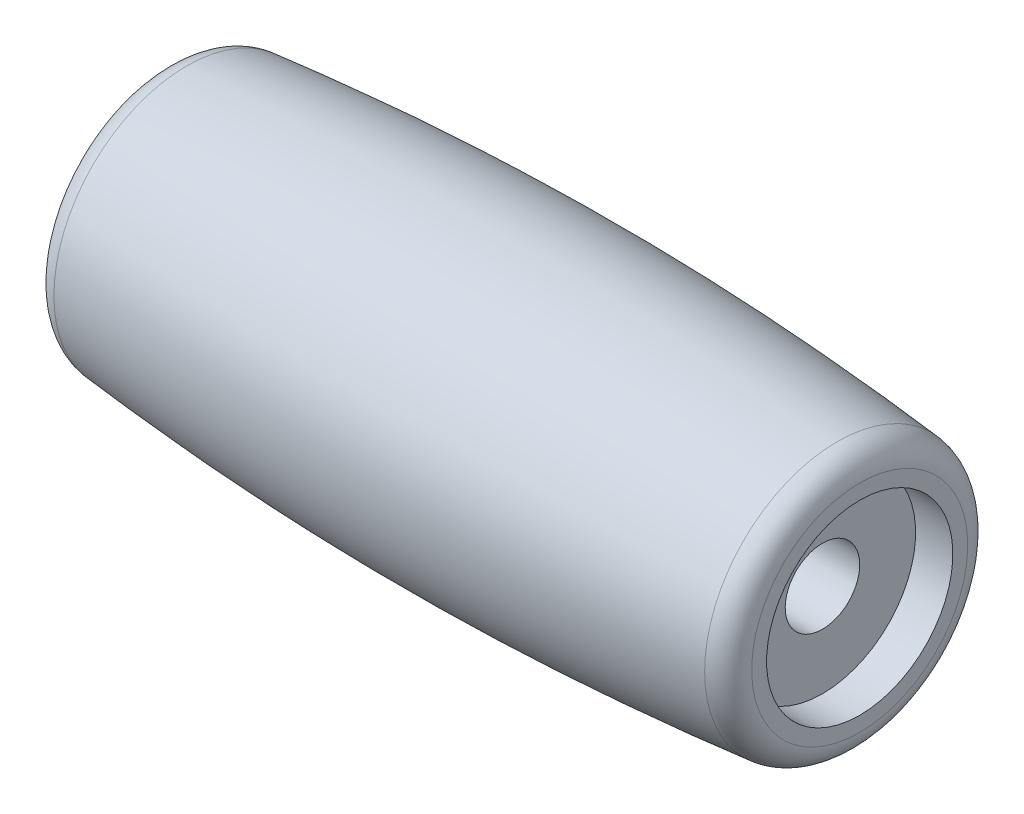
SolidWorks part; units mm, degrees
material "Nylon 101"
ref_plane "Front Plane" through (0, 0, 0) normal (0, 0, 1) x (1, 0, 0)
ref_plane "Top Plane" through (0, 0, 0) normal (0, 1, 0) x (1, 0, 0)
ref_plane "Right Plane" through (0, 0, 0) normal (1, 0, 0) x (0, 0, -1)
sketch "Sketch1" plane through (0, 0, 0) normal (0, 0, 1) x (1, 0, 0)
  line L0 (-75, 0) -> (75, 0) construction
  line L3 (0, 0) -> (0, 6) construction
  line L5 (0, 0) -> (0, 30) construction
  line L6 (-12.5, 1.5) -> (12.5, 1.5)
  line L7 (12.5, 1.5) -> (12.5, 3.75)
  line L8 (12.5, 3.75) -> (14, 3.75)
  line L9 (14, 3.75) -> (14, 4.3484)
  line L10 (-14, 3.75) -> (-14, 4.3484)
  line L11 (-12.5, 3.75) -> (-14, 3.75)
  line L12 (-12.5, 1.5) -> (-12.5, 3.75)
  arc A0 (14, 4.3484) -> (13.0998, 5.3434) centre (13, 4.3484) ccw
  arc A1 (-14, 4.3484) -> (-13.0998, 5.3434) centre (-13, 4.3484) cw
  spline S0 degree 3 poles (13.0998, 5.3434) (8.7333, 5.7813) (0.0007, 6.2188) (-8.7346, 5.7811) (-13.0998, 5.3434) knots 0.032152 0.032152 0.032152 0.032152 0.499995 0.967838 0.967838 0.967838 0.967838
  point P3 (0, 0)
  point P18 (0, 1.5)
  dimension "D1" = 150
  dimension "D9" = 13.0998
  dimension "D3" = 1
  dimension "D2" = 30
  dimension "D4" = 1.5
  dimension "D5" = 3.75
  dimension "D6" = 6
  dimension "D7" = 1.5
  dimension "D8" = 14
  dimension "D10" = 4.3484
revolve "Revolve1" add sketch "Sketch1" angle 360 about L0
